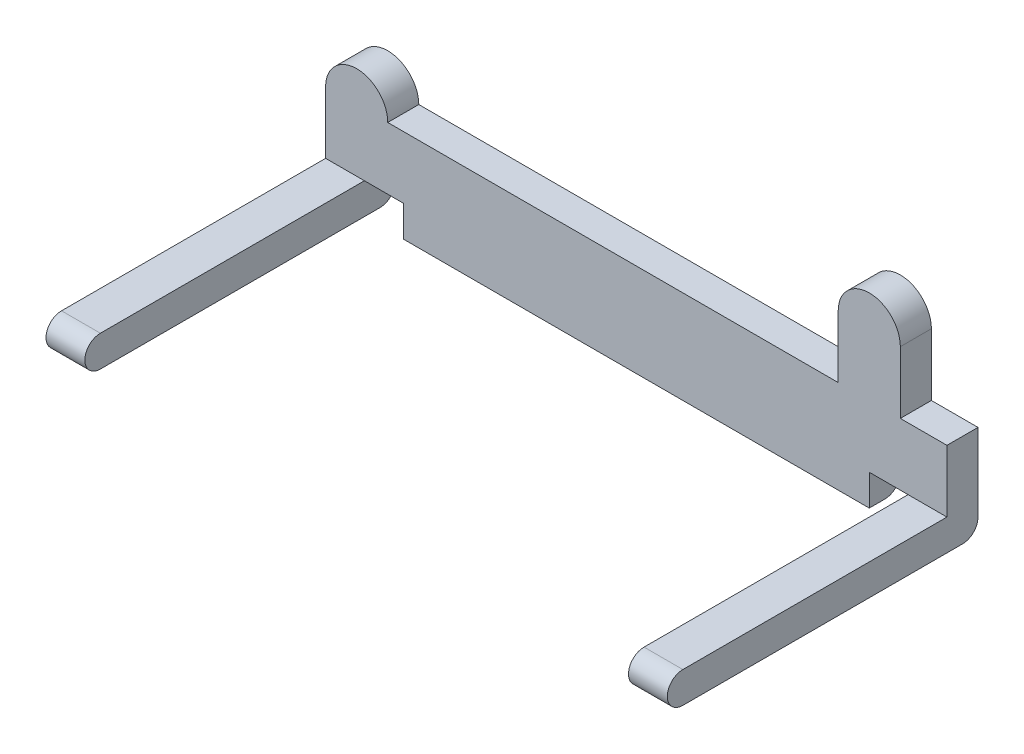
SolidWorks part; units mm, degrees
ref_plane "Front" through (0, 0, 0) normal (0, 0, 1) x (1, 0, 0)
ref_plane "Top" through (0, 0, 0) normal (0, 1, 0) x (1, 0, 0)
ref_plane "Right" through (0, 0, 0) normal (1, 0, 0) x (0, 0, -1)
sketch "草图1" plane through (0, 0, 0) normal (1, 0, 0) x (0, 0, -1)
  line L0 (-18, 0) -> (18, 0) construction
  line L3 (-18, 2) -> (18, 2)
  line L4 (-18, -2) -> (18, -2)
  line L6 (18, 2) -> (20, 2)
  line L7 (20, 2) -> (20, 0)
  arc A6 (-18, 2) -> (-18, -2) centre (-18, 0) ccw
  arc A7 (18, -2) -> (20, 0) centre (18, 0) ccw
  point P2 (0, 0)
  point P4 (0, 0)
extrude "凸台-拉伸1" add sketch "草图1" along normal blind 80
sketch "草图10" plane through (80, 0, 0) normal (1, 0, 0) x (0, 0, -1)
  line L1 (20, 2) -> (16, 2)
  line L2 (20, 2) -> (20, 10)
  line L3 (20, 10) -> (16, 10)
  line L4 (16, 2) -> (16, 10)
  dimension "D1" = 8
  dimension "D2" = 4
extrude "凸台-拉伸8" add sketch "草图10" against normal blind 80
sketch "草图11" plane through (0, 0, -20) normal (0, 0, -1) x (-1, 0, 0)
  line L0 (-40, 10) -> (-40, -15.3556) construction
  line L1 (0, 10) -> (-80, 10) construction
  line L13 (-74, 6) -> (-74, -25.3797) construction
  line L15 (-74, 10) -> (-66, 10)
  line L16 (-74, 10) -> (-74, 18)
  line L18 (-66, 10) -> (-66, 18)
  arc A1 (-66, 18) -> (-74, 18) centre (-70, 18) ccw
  circle A3 centre (-4, 10) radius 4
  dimension "D5" = 8
extrude "凸台-拉伸9" add sketch "草图11" against normal blind 4
sketch "草图12" plane through (0, 2, 0) normal (0, 1, 0) x (1, 0, 0)
  line L0 (0, 16) -> (80, 16) construction
  line L1 (5, 16) -> (75, 16)
  line L2 (5, 16) -> (5, -24.8159)
  line L3 (5, -24.8159) -> (75, -24.8159)
  line L4 (75, 16) -> (75, -24.8159)
  line L5 (40, -20) -> (40, 24.2454) construction
  line L6 (0, -20) -> (80, -20) construction
  dimension "D1" = 70
  dimension "D2" = 35
extrude "切除-拉伸1" cut sketch "草图12" against normal blind 10
sketch "草图13" plane through (0, 0, -16) normal (0, 0, 1) x (1, 0, 0)
  line L0 (75, -2) -> (5, -2) construction
  line L1 (5, 2) -> (10, 2)
  line L2 (5, 2) -> (5, -2)
  line L3 (5, -2) -> (10, -2)
  line L4 (10, 2) -> (10, -2)
  line L6 (75, 2) -> (70, 2)
  line L7 (75, 2) -> (75, -2)
  line L8 (75, -2) -> (70, -2)
  line L9 (70, 2) -> (70, -2)
  dimension "D1" = 5
  dimension "D2" = 5
extrude "切除-拉伸2" cut sketch "草图13" against normal blind 10
